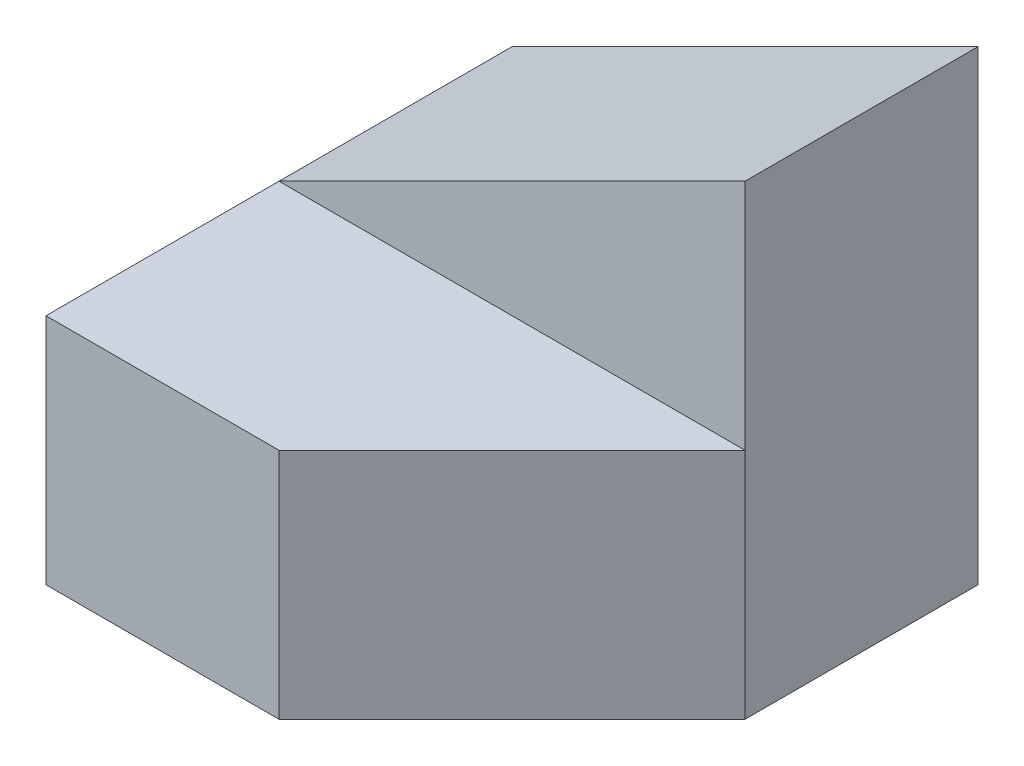
SolidWorks part; units mm, degrees
ref_plane "Front Plane" through (0, 0, 0) normal (0, 0, 1) x (1, 0, 0)
ref_plane "Top Plane" through (0, 0, 0) normal (0, 1, 0) x (1, 0, 0)
ref_plane "Right Plane" through (0, 0, 0) normal (1, 0, 0) x (0, 0, -1)
sketch "Sketch1" plane through (0, 0, 0) normal (0, 0, 1) x (1, 0, 0)
  line L1 (0, 0) -> (40, 0)
  line L2 (0, 0) -> (0, 40)
  line L3 (0, 40) -> (40, 40)
  line L4 (40, 0) -> (40, 40)
  dimension "D1" = 40
  dimension "D2" = 40
extrude "Boss-Extrude1" add sketch "Sketch1" along normal blind 40
sketch "Sketch2" plane through (0, 0, 40) normal (0, 0, 1) x (1, 0, 0)
  line L0 (40, 40) -> (0, 20)
  line L1 (0, 20) -> (0, 40)
  line L2 (0, 40) -> (40, 40)
  dimension "D1" = 20
extrude "Cut-Extrude1" cut sketch "Sketch2" against normal blind 40
sketch "Sketch3" plane through (40, 0, 0) normal (1, 0, 0) x (0, 0, -1)
  line L1 (-40, 40) -> (-20, 40)
  line L2 (-40, 40) -> (-40, 20)
  line L3 (-40, 20) -> (-20, 20)
  line L4 (-20, 40) -> (-20, 20)
  dimension "D1" = 20
  dimension "D2" = 20
extrude "Cut-Extrude2" cut sketch "Sketch3" against normal blind 40
sketch "Sketch4" plane through (0, 20, 0) normal (0, 1, 0) x (1, 0, 0)
  line L0 (40, -20) -> (20, -40)
  line L1 (0, -40) -> (40, -40) construction
  line L2 (20, -40) -> (40, -40)
  line L3 (40, -40) -> (40, -20)
  point P5 (0, 0)
  point P8 (0, 0)
  point P9 (0, 0)
  point P10 (40, -20)
extrude "Cut-Extrude3" cut sketch "Sketch4" against normal blind 40
